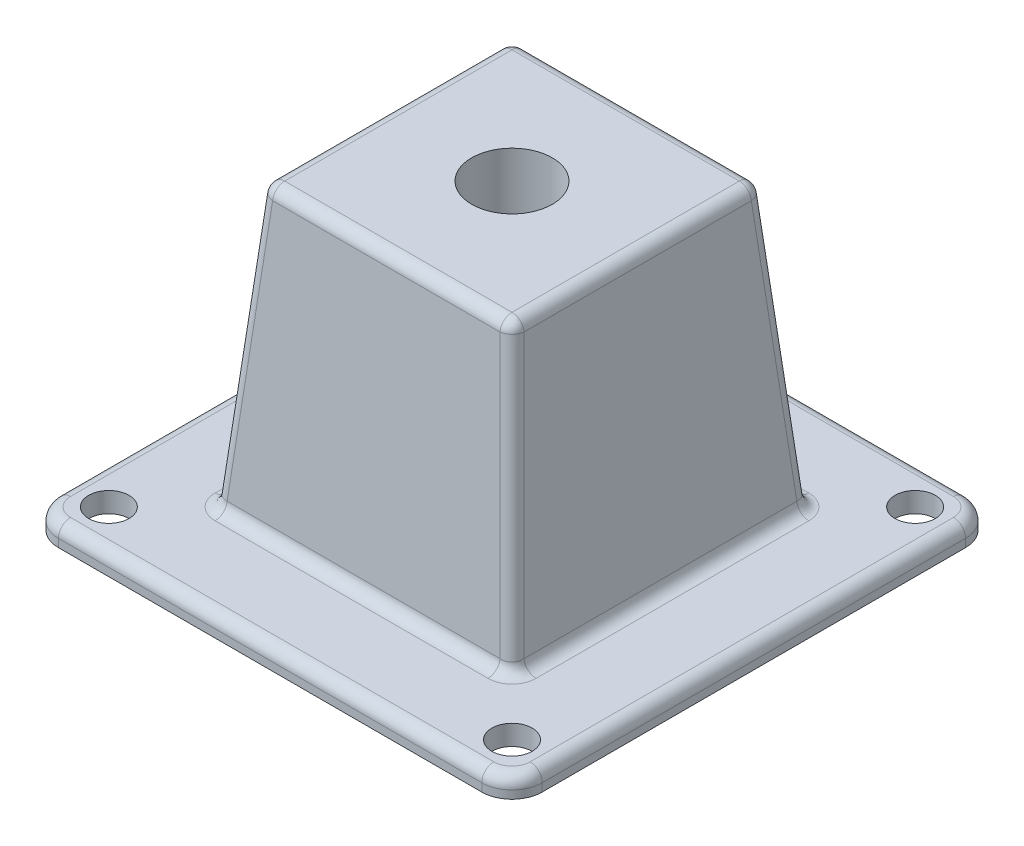
SolidWorks part; units mm, degrees
material "Malleable Cast Iron"
ref_plane "Front Plane" through (0, 0, 0) normal (0, 0, 1) x (1, 0, 0)
ref_plane "Top Plane" through (0, 0, 0) normal (0, 1, 0) x (1, 0, 0)
ref_plane "Right Plane" through (0, 0, 0) normal (1, 0, 0) x (0, 0, -1)
sketch "Sketch1" plane through (0, 0, 0) normal (0, 1, 0) x (1, 0, 0)
  line L0 (0, 0) -> (100, 100) construction
  line L1 (-120, -120) -> (120, -120)
  line L2 (-120, -120) -> (-120, 120)
  line L3 (-120, 120) -> (105, 120)
  line L4 (120, -120) -> (120, 105)
  line L5 (-120, -120) -> (120, 120) construction
  line L6 (-120, 120) -> (120, -120) construction
  circle A0 centre (100, 100) radius 10
  arc A1 (105, 120) -> (120, 105) centre (105, 105) cw
  circle A2 centre (100, -100) radius 10
  arc A3 (120, -105) -> (105, -120) centre (105, -105) cw
  circle A4 centre (-100, -100) radius 10
  arc A5 (-105, -120) -> (-120, -105) centre (-105, -105) cw
  circle A6 centre (-100, 100) radius 10
  arc A7 (-120, 105) -> (-105, 120) centre (-105, 105) cw
  point P0 (0, 0)
  dimension "D3" = 20
  dimension "D6" = 15
  dimension "D1" = 240
  dimension "D2" = 240
  dimension "D4" = 100
  dimension "D5" = 100
  dimension "D8" = 141.4214
  dimension "D7" = 4
extrude "Boss-Extrude1" add sketch "Sketch1" along normal blind 10 contours A7 L2 A5 L1 A3 L4 A1 L3 A6 A4 A2 A0
sketch "Sketch2" plane through (0, 0, 0) normal (0, 1, 0) x (1, 0, 0)
  line L1 (-75, -75) -> (75, -75)
  line L2 (-75, -75) -> (-75, 75)
  line L3 (-75, 75) -> (75, 75)
  line L4 (75, -75) -> (75, 75)
  line L5 (-75, -75) -> (75, 75) construction
  line L6 (-75, 75) -> (75, -75) construction
  point P0 (0, 0)
  dimension "D1" = 150
  dimension "D2" = 150
extrude "Boss-Extrude2" add sketch "Sketch2" along normal blind 150 draft 5
sketch "Sketch3" plane through (0, 0, 0) normal (0, 1, 0) x (1, 0, 0)
  circle A0 centre (0, 0) radius 20
  dimension "D1" = 40
extrude "Cut-Extrude1" cut sketch "Sketch3" along normal through all
fillet "Fillet1" radius 6 20 edges at (115.6066, 10, 115.6066) (0, 10, 120) (-115.6066, 10, 115.6066) (-120, 10, 0) (-115.6066, 10, -115.6066) (0, 10, -120) (115.6066, 10, -115.6066) (-74.1251, 10, 0) (-68.0009, 80, -68.0009) (0, 10, -74.1251) (68.0009, 80, -68.0009) (74.1251, 10, 0) (-68.0009, 80, 68.0009) (68.0009, 80, 68.0009) (0, 10, 74.1251) (0, 150, 61.8767) (-61.8767, 150, 0) (0, 150, -61.8767) (61.8767, 150, 0) (120, 10, 0)
